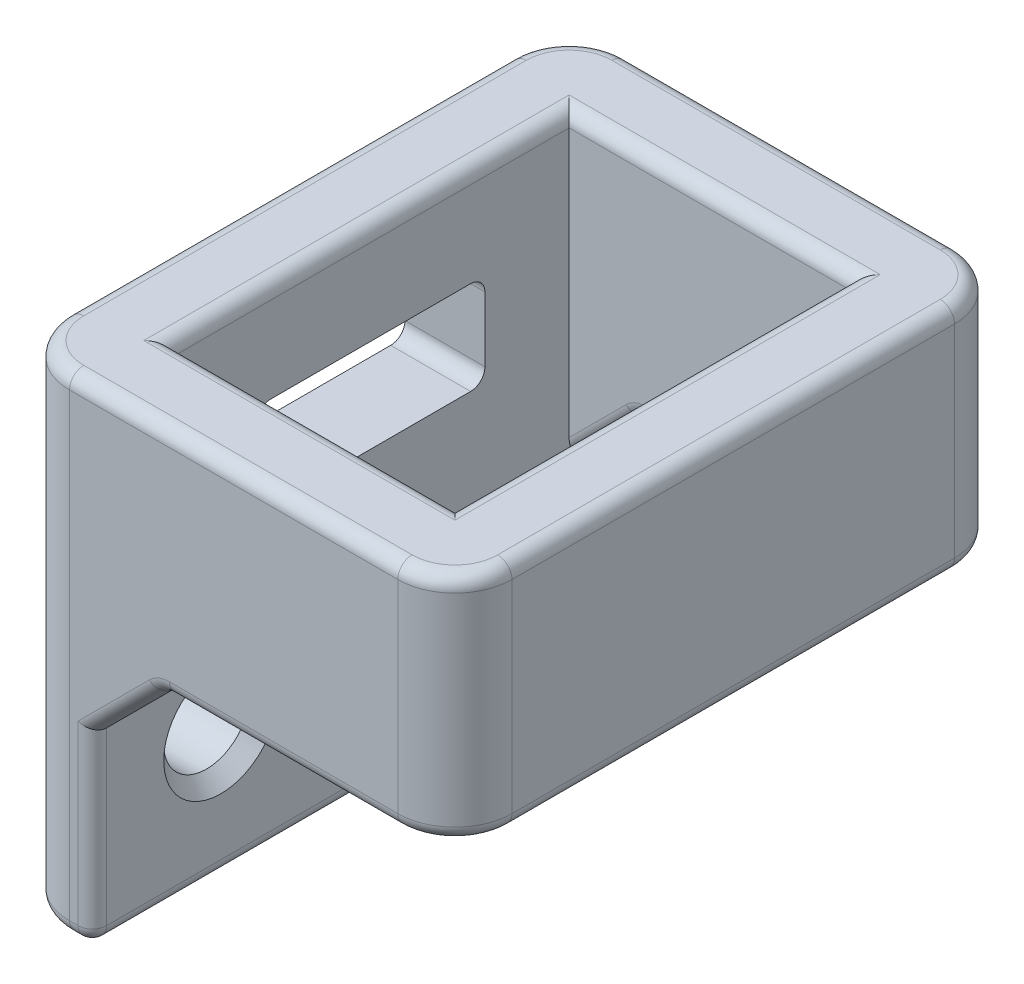
SolidWorks part; units mm, degrees
material "ABS"
ref_plane "Plano frontal" through (0, 0, 0) normal (0, 0, 1) x (1, 0, 0)
ref_plane "Plano superior" through (0, 0, 0) normal (0, 1, 0) x (1, 0, 0)
ref_plane "Plano direito" through (0, 0, 0) normal (1, 0, 0) x (0, 0, -1)
sketch "Sketch1" plane through (0, 0, 0) normal (0, 1, 0) x (1, 0, 0)
  line L0 (-7.75, 9.75) -> (7.75, 9.75)
  line L5 (-4.75, 6.75) -> (4.75, 6.75) construction
  line L6 (-4.75, 6.75) -> (-4.75, -6.75) construction
  line L7 (-4.75, -6.75) -> (4.75, -6.75) construction
  line L8 (4.75, 6.75) -> (4.75, -6.75) construction
  line L9 (7.75, 9.75) -> (7.75, -9.75)
  line L10 (-7.75, -9.75) -> (7.75, -9.75)
  line L11 (-7.75, 9.75) -> (-7.75, -9.75)
  line L12 (-4.95, 6.95) -> (4.95, 6.95)
  line L13 (4.95, 6.95) -> (4.95, -6.95)
  line L14 (-4.95, -6.95) -> (4.95, -6.95)
  line L15 (-4.95, 6.95) -> (-4.95, -6.95)
  point P11 (0, -6.75)
  point P12 (-4.75, 0)
  dimension "D1" = 9.5
  dimension "D2" = 13.5
  dimension "D3" = 3
  dimension "D4" = 0.2
extrude "Boss-Extrude1" add sketch "Sketch1" along normal mid plane 8.1
sketch "Sketch2" plane through (-7.75, 0, 0) normal (-1, 0, 0) x (0, 0, 1)
  line L0 (9.75, 4.05) -> (9.75, -4.05) construction
  line L1 (-9.75, -4.05) -> (9.75, -4.05)
  line L2 (-9.75, -4.05) -> (-9.75, -13.05)
  line L3 (-9.75, -13.05) -> (9.75, -13.05)
  line L4 (9.75, -4.05) -> (9.75, -13.05)
  line L5 (0, -8.525) -> (0, 8.525) construction
  circle A0 centre (-5.25, -8.55) radius 1.5
  circle A2 centre (5.25, -8.55) radius 1.5
  dimension "D1" = 3
  dimension "D2" = 3
  dimension "D3" = 3
  dimension "D4" = 3
extrude "Boss-Extrude2" add sketch "Sketch2" against normal up to surface (2.8 mm away) up to face at (-4.95, 0, 0)
chamfer "Chamfer1" distance 2.5 angle 45 2 edges at (-4.95, -4.05, -8.35) (-4.95, -4.05, 8.35)
fillet "Fillet1" radius 2 4 edges at (-7.75, -4.5, 9.75) (-7.75, -4.5, -9.75) (7.75, 0, -9.75) (7.75, 0, 9.75)
fillet "Fillet2" radius 0.5 34 edges at (-7.1642, -13.05, 9.1642) (-4.95, -13.05, 0) (-7.1642, -13.05, -9.1642) (-7.75, -13.05, 0) (7.1642, -4.05, 9.1642) (7.75, -4.05, 0) (7.1642, -4.05, -9.1642) (-4.95, -9.8, 9.75) (-5.35, -13.05, 9.75) (1.65, -4.05, 9.75) (-5.35, -13.05, -9.75) (-4.95, -9.8, -9.75) (1.65, -4.05, -9.75) (7.1642, 4.05, 9.1642) (0, 4.05, 9.75) (-7.1642, 4.05, 9.1642) (-7.75, 4.05, 0) (-7.1642, 4.05, -9.1642) (0, 4.05, -9.75) (7.1642, 4.05, -9.1642) (7.75, 4.05, 0) (1.25, -4.05, -6.95) (4.95, -4.05, 0) (1.25, -4.05, 6.95) (4.95, 4.05, 0) (0, 4.05, -6.95) (-4.95, 4.05, 0) (0, 4.05, 6.95) (-3.7, -5.3, -6.95) (-3.7, -5.3, 6.95) (-2.45, -4.05, -8.35) (-2.45, -4.05, 8.35) (-3.7, -5.3, 9.75) (-3.7, -5.3, -9.75)
chamfer "Chamfer2" distance 0.5 angle 45 2 edges at (-4.95, -8.55, -6.75) (-4.95, -8.55, 3.75)
sketch "Sketch3" plane through (-7.75, 0, 0) normal (-1, 0, 0) x (0, 0, 1)
  line L0 (-7.75, 4.05) -> (7.75, 4.05) construction
  line L1 (-3.5, 0.55) -> (3.5, 0.55)
  line L2 (-4, 0.05) -> (-4, -2.22)
  line L3 (-3.5, -2.72) -> (3.5, -2.72)
  line L4 (4, 0.05) -> (4, -2.22)
  arc A0 (3.5, -2.72) -> (4, -2.22) centre (3.5, -2.22) ccw
  arc A1 (3.5, 0.55) -> (4, 0.05) centre (3.5, 0.05) cw
  arc A2 (-4, -2.22) -> (-3.5, -2.72) centre (-3.5, -2.22) ccw
  arc A3 (-3.5, 0.55) -> (-4, 0.05) centre (-3.5, 0.05) ccw
  point P6 (0, 0.55)
  point P9 (4, -2.72)
  point P15 (-4, -2.72)
  point P18 (-4, 0.55)
  dimension "D4" = 0.5
  dimension "D1" = 3.5
  dimension "D2" = 3.27
  dimension "D3" = 8
extrude "Cut-Extrude1" cut sketch "Sketch3" along normal through all and the other way up to next
